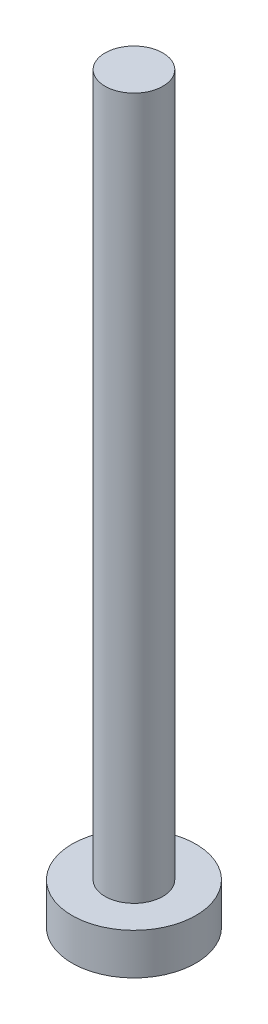
SolidWorks part; units mm, degrees
ref_plane "Front Plane" through (0, 0, 0) normal (0, 0, 1) x (1, 0, 0)
ref_plane "Top Plane" through (0, 0, 0) normal (0, 1, 0) x (1, 0, 0)
ref_plane "Right Plane" through (0, 0, 0) normal (1, 0, 0) x (0, 0, -1)
sketch "Sketch1" plane through (0, 0, 0) normal (0, 0, 1) x (1, 0, 0)
  line L3 (-1.4, 2) -> (-1.4, 36)
  line L4 (-1.4, 36) -> (0, 36)
  line L5 (0, 36) -> (0, 0)
  line L6 (-1.4, 2) -> (-3, 2)
  line L7 (-3, 2) -> (-3, 0)
  line L8 (-3, 0) -> (0, 0)
  dimension "D1" = 1.4
  dimension "D2" = 34
  dimension "D3" = 2
  dimension "D4" = 3
revolve "Revolve1" add sketch "Sketch1" angle 360 about L5
